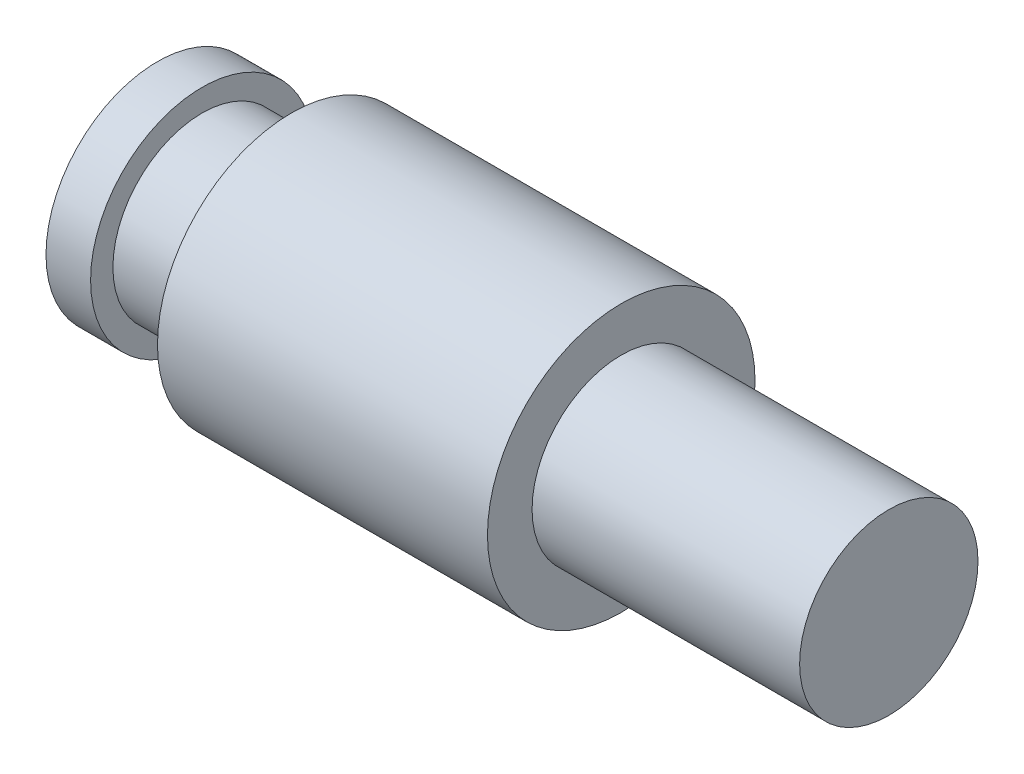
SolidWorks part; units mm, degrees
ref_plane "Face" through (0, 0, 0) normal (0, 0, 1) x (1, 0, 0)
ref_plane "Dessus" through (0, 0, 0) normal (0, 1, 0) x (1, 0, 0)
ref_plane "Droite" through (0, 0, 0) normal (1, 0, 0) x (0, 0, -1)
sketch "Esquisse1" plane through (0, 0, 0) normal (0, 0, 1) x (1, 0, 0)
  line L0 (0, 0) -> (0, 2.5)
  line L1 (0, 2.5) -> (1, 2.5)
  line L2 (1, 2.5) -> (1, 2)
  line L3 (3, 2) -> (3, 3)
  line L4 (3, 3) -> (10.4, 3)
  line L5 (16.4, 2) -> (16.4, 0)
  line L6 (16.4, 0) -> (0, 0)
  line L7 (1, 2) -> (3, 2)
  line L8 (10.4, 3) -> (10.4, 2)
  line L9 (10.4, 2) -> (16.4, 2)
  dimension "D1" = 2.5
  dimension "D2" = 1
  dimension "D3" = 2
  dimension "D4" = 2
  dimension "D5" = 3
  dimension "D6" = 7.4
  dimension "D7" = 2
  dimension "D8" = 13.4
revolve "Révolution1" add sketch "Esquisse1" angle 360 about L6
